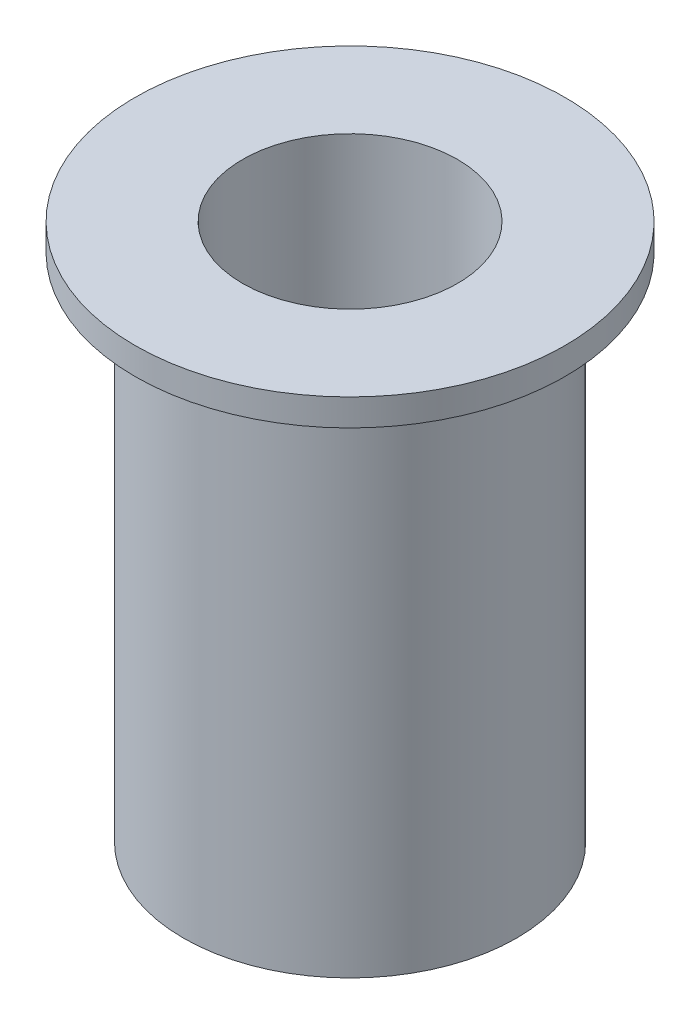
SolidWorks part; units mm, degrees
ref_plane "Front Plane" through (0, 0, 0) normal (0, 0, 1) x (1, 0, 0)
ref_plane "Top Plane" through (0, 0, 0) normal (0, 1, 0) x (1, 0, 0)
ref_plane "Right Plane" through (0, 0, 0) normal (1, 0, 0) x (0, 0, -1)
sketch "Sketch1" plane through (0, 0, 0) normal (0, 0, 1) x (1, 0, 0)
  line L0 (0, 0) -> (2, 0) construction
  line L1 (3.1, 0) -> (3.1, 9.5)
  line L2 (3.1, 9.5) -> (4, 9.5)
  line L3 (4, 9.5) -> (4, 10)
  line L4 (4, 10) -> (2, 10)
  line L5 (0, 10) -> (0, 0) construction
  line L6 (2, 10) -> (2, 0)
  line L7 (2, 10) -> (0, 10) construction
  line L8 (2, 0) -> (3.1, 0)
  dimension "D1" = 10
  dimension "D2" = 4
  dimension "D3" = 3.1
  dimension "D4" = 0.5
  dimension "D5" = 2
revolve "Revolve1" add sketch "Sketch1" angle 360 about L5
